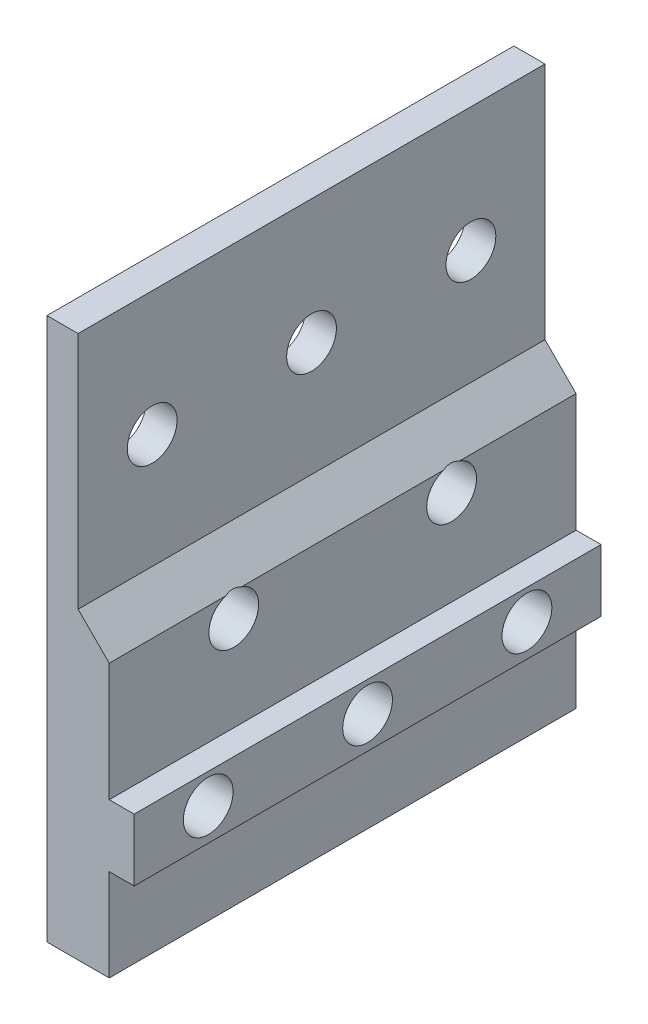
SolidWorks part; units mm, degrees
ref_plane "Front Plane" through (0, 0, 0) normal (0, 0, 1) x (1, 0, 0)
ref_plane "Top Plane" through (0, 0, 0) normal (0, 1, 0) x (1, 0, 0)
ref_plane "Right Plane" through (0, 0, 0) normal (1, 0, 0) x (0, 0, -1)
sketch "Sketch1" plane through (0, 0, 0) normal (0, 0, 1) x (1, 0, 0)
  line L0 (0, 0) -> (0, 55.3466)
  line L1 (0, 55.3466) -> (3.175, 55.3466)
  line L2 (3.175, 55.3466) -> (3.175, 30.988)
  line L3 (3.175, 30.988) -> (6.35, 27.813)
  line L4 (6.35, 27.813) -> (6.35, 15.748)
  line L5 (6.35, 15.748) -> (8.89, 15.748)
  line L6 (8.89, 15.748) -> (8.89, 9.398)
  line L7 (8.89, 9.398) -> (6.35, 9.398)
  line L8 (6.35, 9.398) -> (6.35, 0)
  line L9 (6.35, 0) -> (0, 0)
  dimension "D1" = 55.3466
  dimension "D2" = 9.398
  dimension "D3" = 2.54
  dimension "D4" = 6.35
  dimension "D5" = 135
  dimension "D6" = 6.35
  dimension "D7" = 3.175
  dimension "D8" = 24.3586
extrude "Boss-Extrude1" add sketch "Sketch1" along normal blind 47.625
sketch "Sketch2" plane through (0, 0, 0) normal (-1, 0, 0) x (0, 0, 1)
  line L0 (23.8125, 55.3466) -> (23.8125, 0) construction
  line L1 (47.625, 55.3466) -> (0, 55.3466) construction
  line L2 (47.625, 0) -> (0, 0) construction
  line L3 (7.5565, 42.6466) -> (40.0685, 42.6466) construction
  line L4 (12.7, 25.4) -> (34.925, 25.4) construction
  line L5 (7.5565, 12.7) -> (40.0685, 12.7) construction
  line L6 (0, 55.3466) -> (0, 0) construction
  circle A0 centre (40.0685, 12.7) radius 2.54
  circle A1 centre (7.5565, 12.7) radius 2.54
  circle A2 centre (12.7, 25.4) radius 2.54
  circle A3 centre (34.925, 25.4) radius 2.54
  circle A4 centre (7.5565, 42.6466) radius 2.54
  circle A5 centre (40.0685, 42.6466) radius 2.54
  circle A6 centre (23.8125, 12.7) radius 2.54
  circle A7 centre (23.8125, 42.6466) radius 2.54
  point P18 (23.8125, 42.6466)
  point P19 (23.8125, 25.4)
  point P20 (23.8125, 12.7)
  dimension "D1" = 5.08
  dimension "D2" = 25.4
  dimension "D3" = 12.7
  dimension "D4" = 12.7
  dimension "D5" = 32.512
  dimension "D6" = 12.7
extrude "Cut-Extrude1" cut sketch "Sketch2" against normal through all
